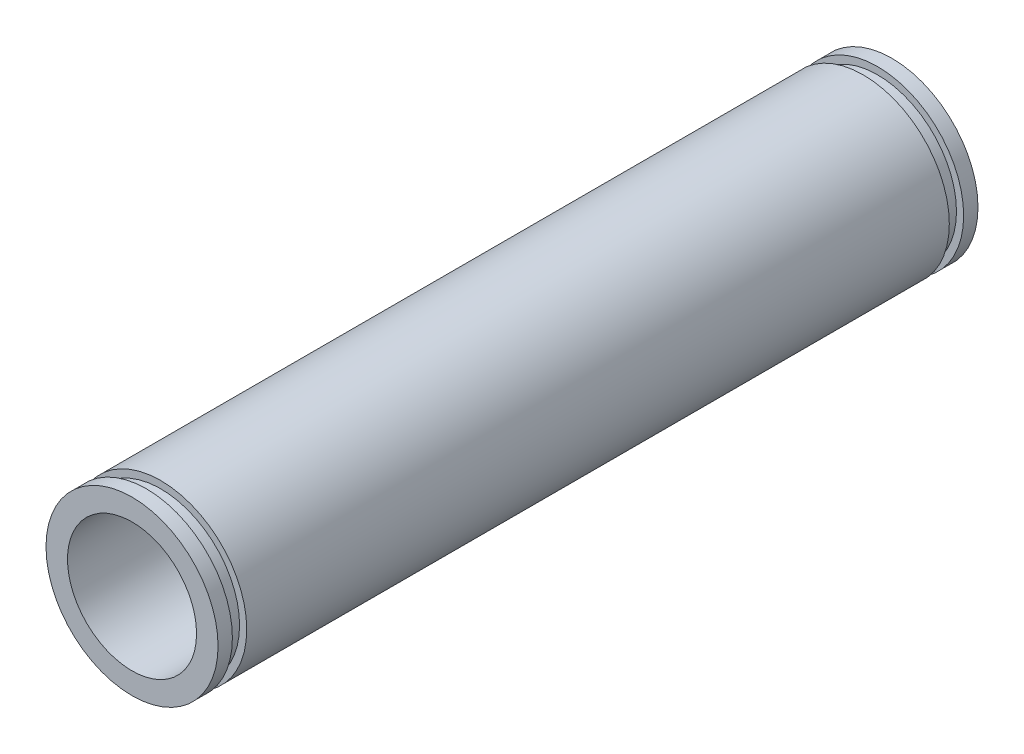
SolidWorks part; units mm, degrees
material "Сталь"
ref_plane "Спереди" through (0, 0, 0) normal (0, 0, 1) x (1, 0, 0)
ref_plane "Сверху" through (0, 0, 0) normal (0, 1, 0) x (1, 0, 0)
ref_plane "Справа" through (0, 0, 0) normal (1, 0, 0) x (0, 0, -1)
sketch "Эскиз1" plane through (0, 0, 0) normal (0, 0, 1) x (1, 0, 0)
  circle A0 centre (0, 0) radius 6
  circle A1 centre (0, 0) radius 4.5
  dimension "D1" = 12
  dimension "D2" = 9
extrude "Бобышка-Вытянуть1" add sketch "Эскиз1" along normal mid plane 53
sketch "Эскиз2" plane through (0, 0, 26.5) normal (0, 0, 1) x (1, 0, 0)
  circle A0 centre (0, 0) radius 5.5
  circle A1 centre (0, 0) radius 6
  circle A2 centre (0, 0) radius 6
  dimension "D1" = 0
  dimension "D2" = 0.5
extrude "Вырез-Вытянуть1" cut sketch "Эскиз2" against normal blind 1 from offset 1 offset against normal yes
mirror "Зеркальное отражение1" about plane through (0, 0, 0) normal (0, 0, 1) of "Вырез-Вытянуть1"
